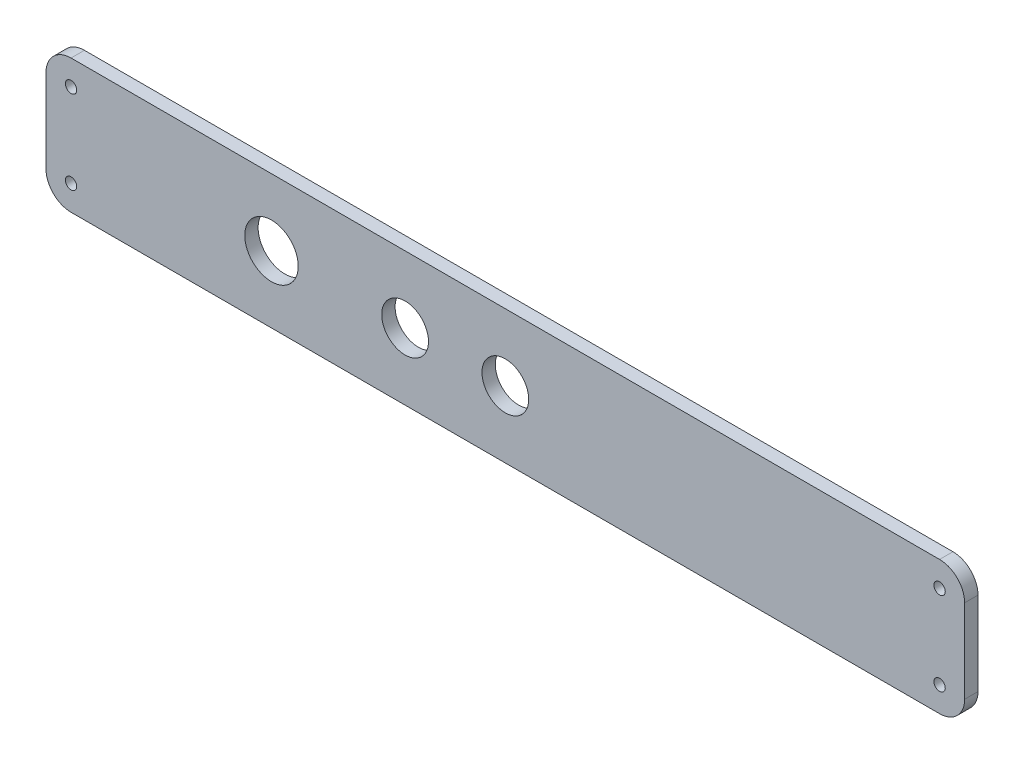
SolidWorks part; units mm, degrees
material "MDF"
ref_plane "正面" through (0, 0, 0) normal (1, 0, 0) x (0, 1, 0)
ref_plane "平面" through (0, 0, 0) normal (0, 0, 1) x (0, 1, 0)
ref_plane "右側面" through (0, 0, 0) normal (0, 1, 0) x (-1, 0, 0)
sketch "ｽｹｯﾁ1" plane through (0, 0, 0) normal (0, 0, 1) x (0, 1, 0)
  line L1 (0, 0) -> (40, 0)
  line L2 (0, 0) -> (0, 275)
  line L3 (0, 275) -> (40, 275)
  line L4 (40, 0) -> (40, 275)
  dimension "D1" = 275
  dimension "D2" = 40
extrude "ﾎﾞｽ - 押し出し1" add sketch "ｽｹｯﾁ1" along normal blind 4
sketch "ｽｹｯﾁ2" plane through (0, 0, 4) normal (0, 0, 1) x (1, 0, 0)
  line L0 (0, 40) -> (-275, 40) construction
  line L1 (-275, 40) -> (-275, 0) construction
  circle A0 centre (-207.5, 20) radius 8
  circle A1 centre (-167.5, 20) radius 7
  circle A2 centre (-137.5, 20) radius 7
  point P8 (-137.5, 40)
  point P12 (-275, 20)
  dimension "D1" = 16
  dimension "D2" = 14
  dimension "D3" = 70
  dimension "D4" = 40
  dimension "D5" = 30
extrude "ｶｯﾄ - 押し出し1" cut sketch "ｽｹｯﾁ2" against normal through all
sketch "ｽｹｯﾁ3" plane through (0, 0, 4) normal (0, 0, 1) x (1, 0, 0)
  line L0 (-275, 40) -> (-275, 0) construction
  line L1 (-137.5, 40) -> (-137.5, 0) construction
  line L2 (0, 40) -> (-275, 40) construction
  line L3 (-275, 0) -> (0, 0) construction
  point P0 (-267.5, 32.5)
  point P1 (-267.5, 7.5)
  point P6 (-275, 20)
  point P14 (-7.5, 7.5)
  point P15 (-7.5, 32.5)
  dimension "D1" = 25
  dimension "D2" = 12.5
  dimension "D3" = 7.5
hole_wizard "M3 すきま穴1" positions "ｽｹｯﾁ3" profile "ｽｹｯﾁ4" hole size "M3" standard "JIS" end condition through all
sketch "ｽｹｯﾁ4" plane through (-267.5, 32.5, 4) normal (1, 0, 0) x (0, -1, 0)
  line L0 (0, 0) -> (0, 4)
  line L1 (0, 4) -> (1.7, 4)
  line L2 (1.7, 4) -> (1.7, 0)
  line L5 (1.7, 0) -> (0, 0)
  line L11 (0, -6.35) -> (0, 107.95) construction
  dimension "通し穴の直径" = 3.4
  dimension "通し穴の深さ" = 4
fillet "ﾌｨﾚｯﾄ1" radius 7.5 4 edges at (0, 40, 2) (0, 0, 2) (-275, 40, 2) (-275, 0, 2)
equation "\"D2@ｽｹｯﾁ3\"= \"D1@ｽｹｯﾁ3\" / 2"
